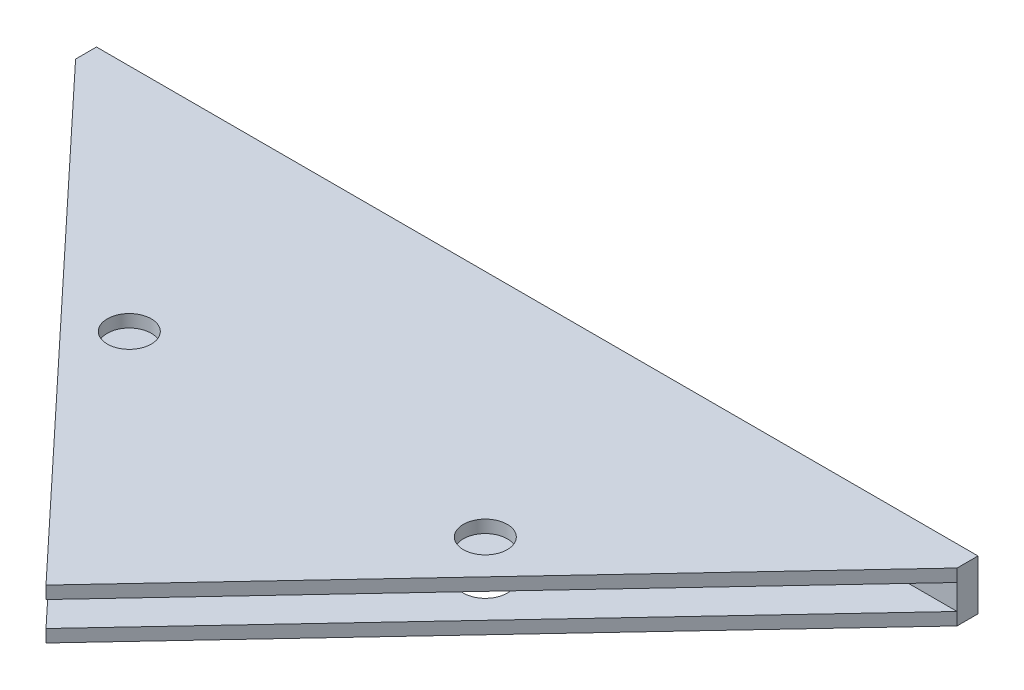
SolidWorks part; units mm, degrees
ref_plane "Front Plane" through (0, 0, 0) normal (0, 0, 1) x (1, 0, 0)
ref_plane "Top Plane" through (0, 0, 0) normal (0, 1, 0) x (1, 0, 0)
ref_plane "Right Plane" through (0, 0, 0) normal (1, 0, 0) x (0, 0, -1)
sketch "Sketch1" plane through (0, 0, 0) normal (0, 1, 0) x (1, 0, 0)
  line L0 (39.4127, 0.6403) -> (-2.757, 45.6403)
  line L2 (-2.757, 45.6403) -> (39.4127, 45.6403)
  line L3 (39.4127, 45.6403) -> (39.4127, 0.6403)
  line L4 (-2.757, 45.6403) -> (-2.757, 47.6403)
  line L5 (-2.757, 47.6403) -> (39.4127, 47.6403)
  line L6 (39.4127, 47.6403) -> (39.4127, 45.6403)
  circle A0 centre (22.3813, 25.641) radius 2.1
  dimension "D1" = 2
sketch "Sketch4" plane through (0, 0, 0) normal (0, 1, 0) x (1, 0, 0)
  line L0 (-2.757, 47.6403) -> (81.5825, 47.6403)
  line L1 (39.4127, 47.6403) -> (39.4127, 0.6403)
  line L2 (39.4127, 0.6403) -> (-2.757, 45.6403)
  line L3 (-2.757, 45.6403) -> (-2.757, 47.6403)
  line L4 (39.4127, 0.6403) -> (81.5825, 45.6403)
  line L5 (81.5825, 45.6403) -> (81.5825, 47.6403)
  circle A0 centre (22.3813, 25.641) radius 2.1
  circle A1 centre (56.4442, 25.641) radius 2.1
extrude "Boss-Extrude3" add sketch "Sketch4" along normal blind 1.2 contours L3 L2 L1 L0 A0 | L4 L5 L0 L1 A1
sketch "Sketch5" plane through (0, 0, 0) normal (0, -1, 0) x (-1, 0, 0)
  line L1 (2.757, 45.6403) -> (-81.5825, 45.6403)
  line L2 (2.757, 45.6403) -> (2.757, 47.6403)
  line L3 (2.757, 47.6403) -> (-81.5825, 47.6403)
  line L4 (-81.5825, 45.6403) -> (-81.5825, 47.6403)
extrude "Boss-Extrude4" add sketch "Sketch5" along normal blind 2.4
sketch "Sketch6" plane through (0, -2.4, 0) normal (0, -1, 0) x (-1, 0, 0)
  line L0 (2.757, 47.6403) -> (-81.5825, 47.6403)
  line L1 (-81.5825, 47.6403) -> (-81.5825, 45.6403)
  line L2 (-81.5825, 45.6403) -> (-39.4127, 0.6403)
  line L3 (-39.4127, 0.6403) -> (2.757, 45.6403)
  line L4 (2.757, 45.6403) -> (2.757, 47.6403)
  circle A0 centre (-22.3813, 25.641) radius 2.1
  circle A1 centre (-56.4442, 25.641) radius 2.1
extrude "Boss-Extrude5" add sketch "Sketch6" along normal blind 1.2
